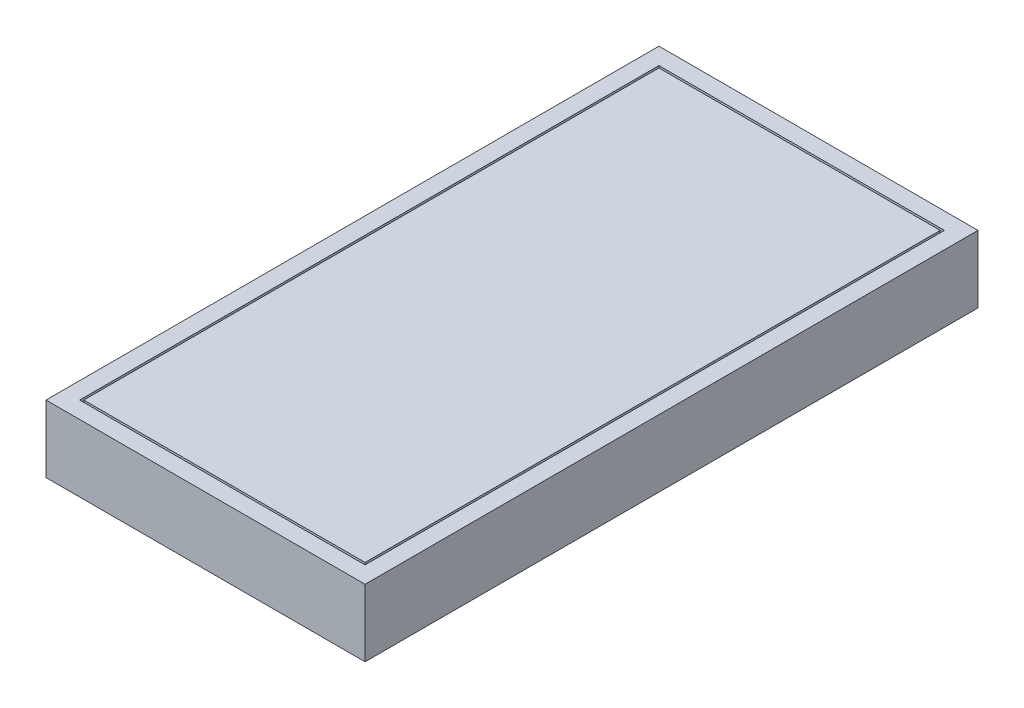
SolidWorks part; units mm, degrees
ref_plane "Front Plane" through (0, 0, 0) normal (0, 0, 1) x (1, 0, 0)
ref_plane "Top Plane" through (0, 0, 0) normal (0, 1, 0) x (1, 0, 0)
ref_plane "Right Plane" through (0, 0, 0) normal (1, 0, 0) x (0, 0, -1)
ref_plane "Plane1" through (0, -60, 0) normal (0, -1, 0) x (1, 0, 0)
sketch "Sketch1" plane through (0, -60, 0) normal (0, -1, 0) x (1, 0, 0)
  line L0 (-190, 0) -> (190, 0)
  line L1 (190, 0) -> (190, 730)
  line L2 (190, 730) -> (-190, 730)
  line L3 (-190, 730) -> (-190, 0)
  dimension "D1" = 730
  dimension "D2" = 190
  dimension "D3" = 380
extrude "Boss-Extrude1" add sketch "Sketch1" against normal blind 80
sketch "Sketch2" plane through (0, 20, 0) normal (0, 1, 0) x (-1, 0, 0)
  line L0 (170, 710) -> (-170, 710)
  line L1 (-170, 710) -> (-170, 20)
  line L2 (-170, 20) -> (170, 20)
  line L3 (170, 20) -> (170, 710)
  dimension "D1" = 20
  dimension "D2" = 690
  dimension "D3" = 170
  dimension "D4" = 340
extrude "Cut-Extrude1" cut sketch "Sketch2" against normal blind 11
sketch "Sketch3" plane through (0, 9, 0) normal (0, 1, 0) x (-1, 0, 0)
  line L0 (167.5, 707.5) -> (167.5, 22.5)
  line L1 (167.5, 22.5) -> (-167.5, 22.5)
  line L2 (-167.5, 22.5) -> (-167.5, 707.5)
  line L3 (-167.5, 707.5) -> (167.5, 707.5)
  line L4 (-170, 20) -> (170, 20) construction
  line L5 (170, 20) -> (170, 710) construction
  dimension "D1" = 2.5
  dimension "D2" = 685
  dimension "D3" = 2.5
  dimension "D4" = 335
extrude "Boss-Extrude2" add sketch "Sketch3" along normal blind 11
